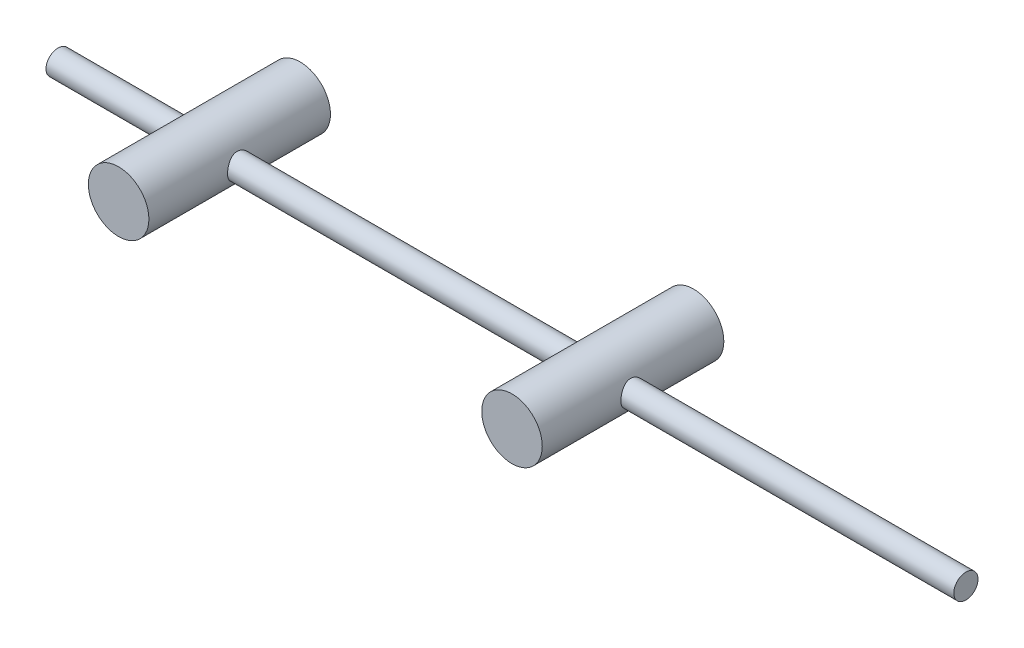
SolidWorks part; units mm, degrees
ref_plane "Plan de face" through (0, 0, 0) normal (0, 0, 1) x (1, 0, 0)
ref_plane "Plan de dessus" through (0, 0, 0) normal (0, 1, 0) x (1, 0, 0)
ref_plane "Plan de droite" through (0, 0, 0) normal (1, 0, 0) x (0, 0, -1)
sketch "Esquisse1" plane through (0, 0, 0) normal (0, 0, 1) x (1, 0, 0)
  line L0 (0, 0) -> (70.413, 0) construction
  line L1 (0, 0) -> (0, 2)
  line L2 (0, 0) -> (150, 0)
  line L3 (0, 2) -> (150, 2)
  line L4 (150, 0) -> (150, 2)
  dimension "D1" = 2
  dimension "D2" = 150
revolve "Révolution1" add sketch "Esquisse1" angle 360 about L0
sketch "Esquisse2" plane through (0, 0, 0) normal (0, 0, 1) x (1, 0, 0)
  line L0 (0, 0) -> (90, 0) construction
  line L1 (150, -2) -> (150, 2) construction
  circle A0 centre (90, 0) radius 5
  circle A1 centre (25, 0) radius 5
  dimension "D1" = 10
  dimension "D2" = 65
  dimension "D3" = 60
extrude "Extrusion1" add sketch "Esquisse2" along normal mid plane 30
